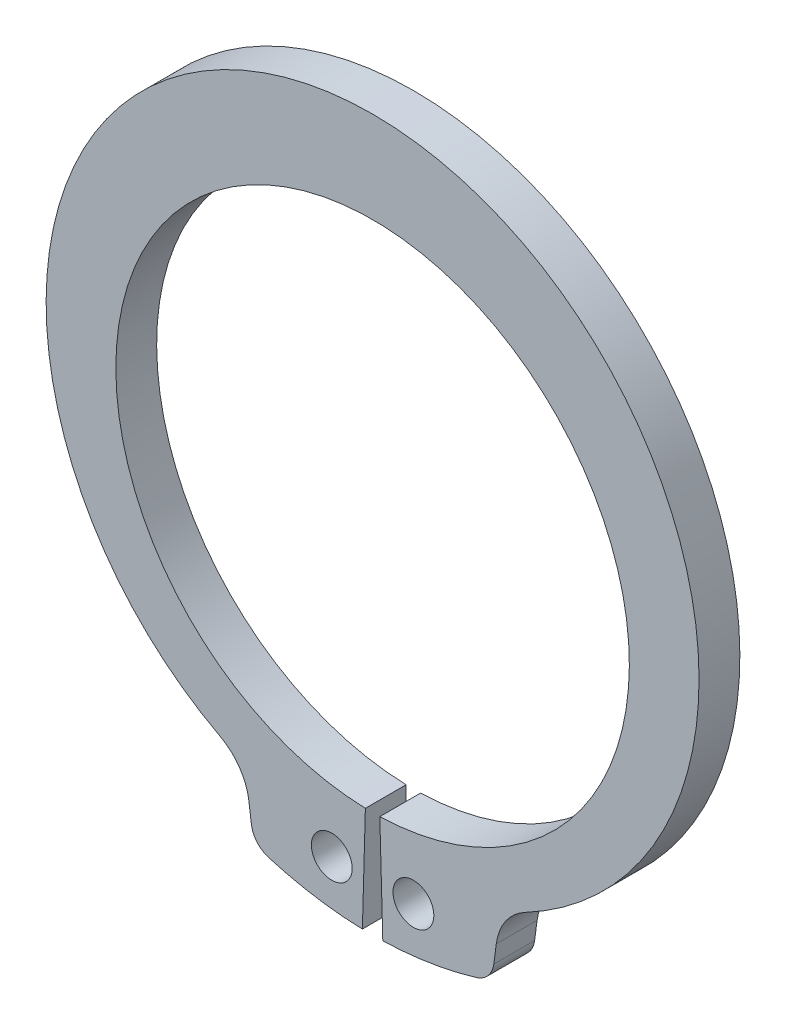
SolidWorks part; units mm, degrees
ref_plane "Plane1" through (0, 0, 0) normal (0, 0, 1) x (1, 0, 0)
ref_plane "Plane2" through (0, 0, 0) normal (0, 1, 0) x (1, 0, 0)
ref_plane "Plane3" through (0, 0, 0) normal (1, 0, 0) x (0, 0, -1)
other "Configuration Table"
sketch "Clipboard" plane through (0, 0, 0) normal (0, 0, 1) x (1, 0, 0)
  line L0 (0, 0) -> (2.8448, 0)
  line L1 (0, 0) -> (0, 1.5748)
  line L2 (0, 0) -> (0, -3.302)
  circle A0 centre (0, 0) radius 0.635
  circle A1 centre (0, 0) radius 8.4963
  dimension "HoleDia" = 1.27
  dimension "ShaftDia" = 16.9926
  dimension "LargeSection" = 2.8448
  dimension "SmallSection" = 1.5748
  dimension "LugSection" = 3.302
sketch "BodySke" plane through (0, 0, 0) normal (0, 0, 1) x (1, 0, 0)
  line L0 (-1.5431, 0) -> (1.5431, 0) construction
  line L1 (0, 0) -> (0, 10.8331) construction
  line L2 (0.2246, -7.9851) -> (0.3175, -11.2858)
  line L3 (-0.2246, -7.9851) -> (-0.3175, -11.2858)
  line L4 (0, 0) -> (5.5599, -9.8264) construction
  line L5 (0, 0) -> (-5.5599, -9.8264) construction
  line L7 (3.8482, -9.6011) -> (3.7712, -10.1866)
  line L8 (-3.8482, -9.6011) -> (-3.7712, -10.1866)
  circle A0 centre (0, 0) radius 7.9883 construction
  arc A1 (0.2246, -7.9851) -> (-0.2246, -7.9851) centre (0, 0) ccw
  arc A2 (4.7093, -8.3232) -> (-4.7093, -8.3232) centre (0, 0.6761) ccw construction
  arc A3 (0.3175, -11.2858) -> (3.2339, -10.8172) centre (0, 0) ccw
  arc A4 (4.7521, -8.3006) -> (3.8482, -9.6011) centre (5.5599, -9.8264) ccw
  arc A5 (-3.8482, -9.6011) -> (-4.7521, -8.3006) centre (-5.5599, -9.8264) ccw
  arc A6 (-3.2339, -10.8172) -> (-0.3175, -11.2858) centre (0, 0) ccw
  arc A7 (4.7521, -8.3006) -> (-4.7521, -8.3006) centre (0, 0.6761) ccw
  arc A8 (-3.9162, -9.0852) -> (3.9162, -9.0852) centre (0, 0) ccw construction
  circle A9 centre (1.27, -9.8114) radius 0.635
  circle A10 centre (-1.27, -9.8114) radius 0.635
  arc A11 (3.7712, -10.1866) -> (3.2339, -10.8172) centre (3.0157, -10.0872) cw
  arc A12 (-3.7712, -10.1866) -> (-3.2339, -10.8172) centre (-3.0157, -10.0872) ccw
  point P28 (3.7083, -10.6639)
  point P31 (-3.7083, -10.6639)
  dimension "GrooveDia" = 15.9766
  dimension "LugRad" = 11.2903
  dimension "HoleOffsetRad" = 9.8933
  dimension "HoleDia" = 1.27
  dimension "D3" = 0.762
  dimension "LargeRad" = 10.8331
  dimension "SmallRad" = 9.5631
  dimension "SmallAngle" = 59.003
  dimension "D2" = 15
  dimension "HoleSpacing" = 2.54
  dimension "Gap" = 0.635
extrude "Body" add sketch "BodySke" against normal blind 1.27
equation "' \"ShaftDia@Clipboard\" = 0.394"
equation "' \"Thickness@Body\" = 0.035"
equation "' \"GrooveDia@BodySke\" = 0.368"
equation "' \"LugSection@Clipboard\" = 0.101"
equation "' \"LargeSection@Clipboard\" = 0.068"
equation "' \"SmallSection@Clipboard\" = 0.039"
equation "' \"HoleDia@Clipboard\" = 0.042"
equation "\"Gap@BodySke\" =  \"Thickness@Body\" / 2"
equation "\"LargeRad@BodySke\" =  \"GrooveDia@BodySke\" / 2 +  \"LargeSection@Clipboard\""
equation "\"SmallRad@BodySke\" =  \"GrooveDia@BodySke\" / 2 +  \"SmallSection@Clipboard\""
equation "\"LugRad@BodySke\" = \"GrooveDia@BodySke\" / 2 + \"LugSection@Clipboard\""
equation "\"HoleOffsetRad@BodySke\" = (  \"ShaftDia@Clipboard\" / 2 + \"LugRad@BodySke\" ) / 2"
equation "\"HoleSpacing@BodySke\" = \"Gap@BodySke\"  * 2 +  \"HoleDia@Clipboard\""
equation "\"HoleDia@BodySke\" =  \"HoleDia@Clipboard\""
equation "\"SmallAngle@BodySke\" = atn(\"HoleSpacing@BodySke\" / 2 / sqr(\"HoleOffsetRad@BodySke\"  * \"HoleOffsetRad@BodySke\" - (\"HoleSpacing@BodySke\" / 2) * (\"HoleSpacing@BodySke\" / 2) ))  * 8 * ( 180 / 3.141593)"
